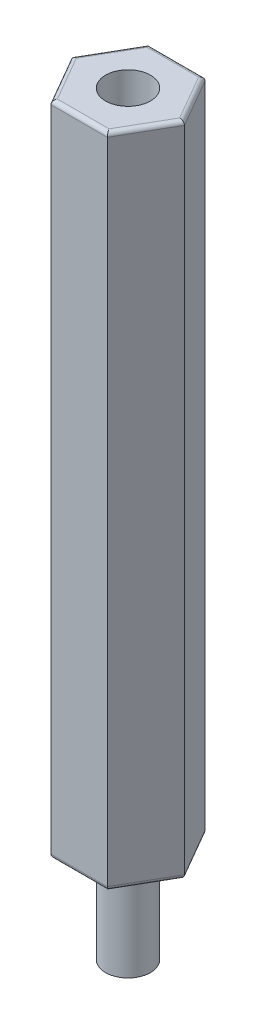
SolidWorks part; units mm, degrees
material "201.0-T43 Molde de fundição com isolamento (SS)"
ref_plane "Plano frontal" through (0, 0, 0) normal (0, 0, 1) x (1, 0, 0)
ref_plane "Plano superior" through (0, 0, 0) normal (0, 1, 0) x (1, 0, 0)
ref_plane "Plano direito" through (0, 0, 0) normal (1, 0, 0) x (0, 0, -1)
sketch "Esboço1" plane through (0, 0, 0) normal (0, 1, 0) x (1, 0, 0)
  line L1 (2.7482, 0) -> (1.3741, 2.38)
  line L2 (1.3741, 2.38) -> (-1.3741, 2.38)
  line L3 (-1.3741, 2.38) -> (-2.7482, 0)
  line L4 (-2.7482, 0) -> (-1.3741, -2.38)
  line L5 (-1.3741, -2.38) -> (1.3741, -2.38)
  line L6 (1.3741, -2.38) -> (2.7482, 0)
  circle A0 centre (0, 0) radius 2.38 construction
  dimension "D1" = 4.76
extrude "Ressalto-extrusão1" add sketch "Esboço1" along normal blind 32
fillet "Filete1" radius 0.2 12 edges at (0, 32, -2.38) (-2.0611, 32, -1.19) (-2.0611, 32, 1.19) (0, 32, 2.38) (2.0611, 32, 1.19) (2.0611, 32, -1.19) (0, 0, 2.38) (-2.0611, 0, 1.19) (-2.0611, 0, -1.19) (0, 0, -2.38) (2.0611, 0, -1.19) (2.0611, 0, 1.19)
sketch "Esboço2" plane through (0, 0, 0) normal (0, -1, 0) x (1, 0, 0)
  circle A0 centre (0, 0) radius 1.0922
  dimension "D1" = 2.1844
extrude "Ressalto-extrusão2" add sketch "Esboço2" along normal blind 4.76
sketch "Esboço3" plane through (0, 32, 0) normal (0, 1, 0) x (1, 0, 0)
  circle A0 centre (0, 0) radius 1.0922
  dimension "D1" = 2.1844
extrude "Corte-extrusão1" cut sketch "Esboço3" against normal blind 4.76
